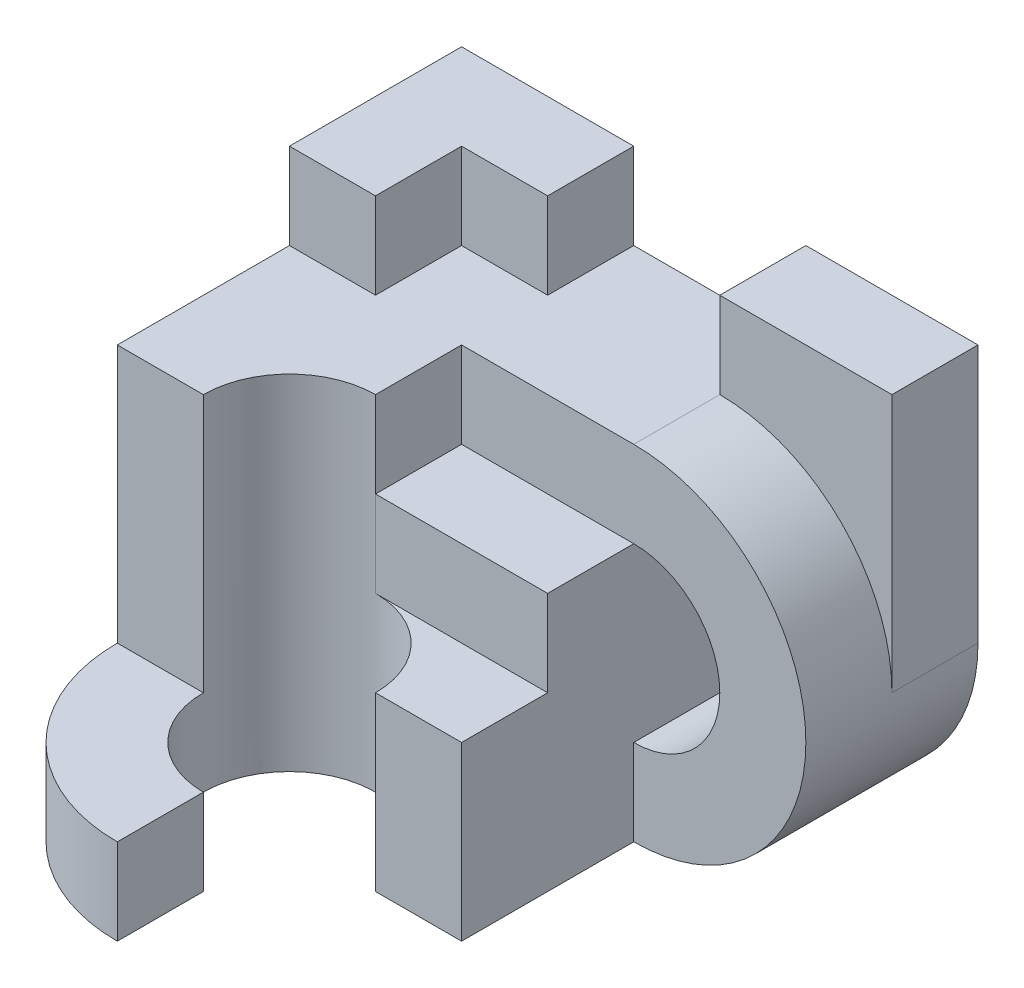
SolidWorks part; units mm, degrees
ref_plane "Front Plane" through (0, 0, 0) normal (0, 0, 1) x (1, 0, 0)
ref_plane "Top Plane" through (0, 0, 0) normal (0, 1, 0) x (1, 0, 0)
ref_plane "Right Plane" through (0, 0, 0) normal (1, 0, 0) x (0, 0, -1)
sketch "Sketch1" plane through (0, 0, 0) normal (0, 0, 1) x (1, 0, 0)
  line L1 (-7.5, -7.5) -> (7.5, -7.5)
  line L2 (-7.5, -7.5) -> (-7.5, 7.5)
  line L3 (-7.5, 7.5) -> (7.5, 7.5)
  line L4 (7.5, -7.5) -> (7.5, 7.5)
  line L5 (-7.5, -7.5) -> (7.5, 7.5) construction
  line L6 (-7.5, 7.5) -> (7.5, -7.5) construction
  point P0 (0, 0)
  dimension "D1" = 15
  dimension "D2" = 15
extrude "Boss-Extrude1" add sketch "Sketch1" along normal blind 15
sketch "Sketch2" plane through (0, 0, 0) normal (0, 0, 1) x (1, 0, 0)
  line L0 (7.5, 12.5) -> (-2.5, 12.5)
  line L1 (7.5, -7.5) -> (7.5, 7.5) construction
  line L2 (7.5, 7.5) -> (-2.5, 7.5)
  line L3 (7.5, 7.5) -> (-7.5, 7.5) construction
  line L4 (-2.5, 12.5) -> (-2.5, 7.5)
  line L5 (7.5, -2.5) -> (7.5, -7.5)
  arc A0 (7.5, -7.5) -> (7.5, 12.5) centre (7.5, 2.5) ccw
  arc A1 (7.5, -2.5) -> (7.5, 7.5) centre (7.5, 2.5) ccw
  dimension "D1" = 10
  dimension "D5" = 5
  dimension "D2" = 5
  dimension "D3" = 20
  dimension "D4" = 10
  dimension "D6" = 10
extrude "Boss-Extrude2" add sketch "Sketch2" along normal blind 10
sketch "Sketch3" plane through (0, 7.5, 0) normal (0, 1, 0) x (1, 0, 0)
  line L1 (-2.5, 0) -> (-7.5, 0)
  line L2 (-2.5, 0) -> (-2.5, -15)
  line L3 (-2.5, -15) -> (-7.5, -15)
  line L4 (-7.5, 0) -> (-7.5, -15)
extrude "Boss-Extrude3" add sketch "Sketch3" along normal blind 5
ref_plane "Plane1" through (0, -7.5, 0) normal (0, 1, 0) x (1, 0, 0)
sketch "Sketch5" plane through (0, -7.5, 0) normal (0, 1, 0) x (1, 0, 0)
  line L1 (-7.5, 0) -> (-12.5, 0)
  line L2 (-7.5, 0) -> (-7.5, -15)
  line L3 (-7.5, -15) -> (-12.5, -15)
  line L4 (-12.5, 0) -> (-12.5, -15)
  dimension "D1" = 15
  dimension "D2" = 5
extrude "Boss-Extrude4" add sketch "Sketch5" along normal blind 20
sketch "Sketch6" plane through (0, -7.5, 0) normal (0, 1, 0) x (1, 0, 0)
  line L0 (-12.5, -15) -> (-12.5, -20)
  line L1 (-12.5, -20) -> (-7.5, -20)
  line L2 (-12.5, -15) -> (-2.5, -15)
  arc A0 (-7.5, -20) -> (-2.5, -15) centre (-2.5, -20) cw
  dimension "D3" = 5
  dimension "D1" = 5
  dimension "D2" = 5
extrude "Boss-Extrude5" add sketch "Sketch6" along normal blind 20
ref_plane "Plane2" through (0, -7.5, 0) normal (0, 1, 0) x (1, 0, 0)
sketch "Sketch7" plane through (0, -7.5, 0) normal (0, 1, 0) x (1, 0, 0)
  line L0 (-2.5, -25) -> (-2.5, -30)
  line L1 (-12.5, -20) -> (-7.5, -20)
  arc A0 (-12.5, -20) -> (-2.5, -30) centre (-2.5, -20) ccw
  arc A1 (-7.5, -20) -> (-2.5, -25) centre (-2.5, -20) ccw
  dimension "D1" = 10
  dimension "D2" = 10
  dimension "D3" = 10
extrude "Boss-Extrude6" add sketch "Sketch7" along normal blind 5
sketch "Sketch8" plane through (0, -7.5, 0) normal (0, 1, 0) x (1, 0, 0)
  line L0 (7.5, -15) -> (7.5, -20)
  line L1 (7.5, -20) -> (2.5, -20)
  line L2 (-2.5, -15) -> (-2.5, -10) construction
  line L3 (-2.5, -15) -> (7.5, -15)
  arc A0 (2.5, -20) -> (-2.5, -15) centre (-2.5, -20) ccw
  dimension "D1" = 5
  dimension "D2" = 5
extrude "Boss-Extrude7" add sketch "Sketch8" along normal blind 10
ref_plane "Plane4" through (0, 2.5, 0) normal (0, 1, 0) x (1, 0, 0)
sketch "Sketch12" plane through (0, 2.5, 0) normal (0, 1, 0) x (1, 0, 0)
  line L0 (7.5, -10) -> (7.5, 0) construction
  line L1 (17.5, 0) -> (7.5, 0)
  line L2 (17.5, 0) -> (17.5, -5)
  line L3 (17.5, -5) -> (7.5, -5)
  line L4 (7.5, 0) -> (7.5, -5)
extrude "Boss-Extrude8" add sketch "Sketch12" along normal blind 15
sketch "Sketch13" plane through (0, 0, 5) normal (0, 0, 1) x (1, 0, 0)
  line L0 (12.5, 2.5) -> (7.5, 2.5)
  line L1 (7.5, 2.5) -> (7.5, 7.5)
  arc A0 (7.5, -2.5) -> (7.5, 7.5) centre (7.5, 2.5) ccw construction
  spline S0 degree 2 poles (7.5, 7.5) (11.0355, 7.5) (12.5, 2.5) knots 0 0 0 1 1 1
extrude "Cut-Extrude1" cut sketch "Sketch13" against normal blind 15
sketch "Sketch14" plane through (0, 12.5, 0) normal (0, 1, 0) x (1, 0, 0)
  line L0 (-12.5, 0) -> (-2.5, 0)
  line L1 (7.5, 0) -> (-12.5, 0) construction
  line L2 (-2.5, 0) -> (-2.5, -5)
  line L3 (-2.5, -5) -> (-7.5, -5)
  line L4 (-7.5, -5) -> (-7.5, -10)
  line L5 (-7.5, -10) -> (-12.5, -10)
  line L6 (-12.5, 0) -> (-12.5, -20) construction
  line L7 (-12.5, -10) -> (-12.5, 0)
  dimension "D1" = 10
  dimension "D2" = 10
  dimension "D3" = 5
  dimension "D4" = 5
extrude "Boss-Extrude9" add sketch "Sketch14" along normal blind 5
